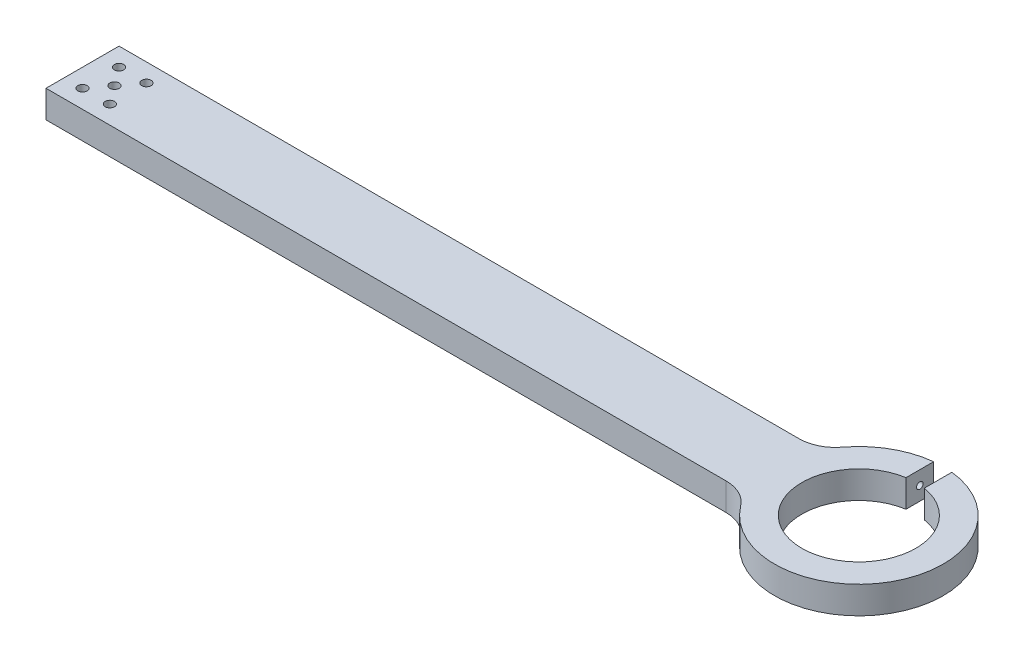
SolidWorks part; units mm, degrees
ref_plane "Front" through (0, 0, 0) normal (0, 0, 1) x (1, 0, 0)
ref_plane "Top" through (0, 0, 0) normal (0, 1, 0) x (1, 0, 0)
ref_plane "Right" through (0, 0, 0) normal (1, 0, 0) x (0, 0, -1)
sketch "Sketch2" plane through (0, 0, 0) normal (0, 1, 0) x (1, 0, 0)
  line L0 (266.825, 19.5688) -> (266.825, 29.1775)
  line L1 (0, 12.7) -> (243.5403, 12.7)
  line L2 (0, 12.7) -> (0, -12.7)
  line L3 (0, -12.7) -> (243.5403, -12.7)
  line L5 (273.175, 29.1775) -> (273.175, 19.5688)
  arc A0 (243.5403, 12.7) -> (266.825, 29.1775) centre (270, 0) cw
  arc A1 (266.825, 19.5688) -> (273.175, 19.5688) centre (270, 0) ccw
  arc A2 (273.175, 29.1775) -> (243.5403, -12.7) centre (270, 0) cw
  point P4 (0, 0)
  dimension "D2" = 39.6494
  dimension "D3" = 9.525
  dimension "D1" = 25.4
  dimension "D4" = 270
  dimension "D5" = 6.35
extrude "Boss-Extrude1" add sketch "Sketch2" along normal mid plane 9.525
hole_wizard "#4-40 Tapped Hole1" positions "Sketch7" profile "Sketch8" tap size "#4-40" standard "ANSI Inch"
sketch "Sketch7" plane through (266.825, 0, 0) normal (1, 0, 0) x (0, 0, -1)
  line L0 (19.5688, 4.7625) -> (29.1775, 4.7625) construction
  line L1 (29.1775, 4.7625) -> (29.1775, -4.7625) construction
  point P0 (24.3731, 0)
  point P6 (24.3731, 4.7625)
  point P10 (29.1775, 0)
sketch "Sketch8" plane through (266.825, 0, -24.3731) normal (0, 1, 0) x (0, 0, -1)
  line L0 (0, 0) -> (0, 266.825)
  line L1 (0, 266.825) -> (1.1303, 266.825)
  line L2 (1.1303, 266.825) -> (1.1303, 0)
  line L5 (1.1303, 0) -> (0, 0)
  line L11 (0, -6.35) -> (0, 107.95) construction
  dimension "Thru Tap Drill Dia." = 2.2606
  dimension "Thru Tap Drill Depth" = 266.825
cosmetic thread "Hole Thread1" parameters "D2"=2.8448
hole_wizard "#4-40 Tapped Hole2" positions "Sketch9" profile "Sketch10" tap size "#4-40" standard "ANSI Inch" end condition through all
sketch "Sketch9" plane through (273.175, 0, 0) normal (-1, 0, 0) x (0, 0, 1)
  line L0 (-29.1775, 4.7625) -> (-29.1775, -4.7625) construction
  line L1 (-29.1775, -4.7625) -> (-19.5688, -4.7625) construction
  point P0 (-24.3731, 0)
  point P5 (-29.1775, 0)
  point P8 (-24.3731, -4.7625)
sketch "Sketch10" plane through (273.175, 0, -24.3731) normal (0, 1, 0) x (0, 0, 1)
  line L0 (0, 0) -> (0, 26.1747)
  line L1 (0, 26.1747) -> (1.1303, 26.1747)
  line L2 (1.1303, 26.1747) -> (1.1303, 0)
  line L5 (1.1303, 0) -> (0, 0)
  line L11 (0, -6.35) -> (0, 107.95) construction
  dimension "Thru Tap Drill Dia." = 2.2606
  dimension "Thru Tap Drill Depth" = 26.1747
cosmetic thread "Hole Thread2" parameters "D2"=2.8448
fillet "Fillet2" radius 12.7 2 edges at (243.5403, 0, -12.7) (243.5403, 0, 12.7)
sketch "Sketch11" plane through (273.175, 0, 0) normal (-1, 0, 0) x (0, 0, 1)
  circle A0 centre (-24.3731, 0) radius 2.413
  dimension "D1" = 4.826
extrude "Cut-Extrude1" cut sketch "Sketch11" against normal through all from offset 9.525 offset against normal yes
hole_wizard "#4 Clearance Hole1" positions "Sketch12" profile "Sketch13" hole size "#4" standard "ANSI Inch" end condition through all
sketch "Sketch12" plane through (0, -4.7625, 0) normal (0, -1, 0) x (-1, 0, 0)
  line L1 (-6.35, -6.35) -> (-15.875, -6.35)
  line L2 (-6.35, -6.35) -> (-6.35, 6.35)
  line L3 (-6.35, 6.35) -> (-15.875, 6.35)
  line L4 (-15.875, -6.35) -> (-15.875, 6.35)
  line L5 (0, -12.7) -> (-236.4886, -12.7) construction
  line L6 (0, 12.7) -> (0, -12.7) construction
  point P0 (-6.35, -6.35)
  point P3 (-15.875, 6.35)
  point P11 (-15.875, -6.35)
  point P13 (-11.1125, 0)
  point P15 (-6.35, 6.35)
  point P75 (-6.35, 0)
  point P76 (-11.1125, -6.35)
  dimension "D1" = 6.35
  dimension "D2" = 12.7
  dimension "D3" = 9.525
  dimension "D4" = 6.35
sketch "Sketch13" plane through (6.35, -4.7625, 6.35) normal (1, 0, 0) x (0, 0, -1)
  line L0 (0, 0) -> (0, 9.525)
  line L1 (0, 9.525) -> (1.6319, 9.525)
  line L2 (1.6319, 9.525) -> (1.6319, 0)
  line L5 (1.6319, 0) -> (0, 0)
  line L11 (0, -6.35) -> (0, 107.95) construction
  dimension "Thru Hole Dia." = 3.2639
  dimension "Thru Hole Depth" = 9.525
